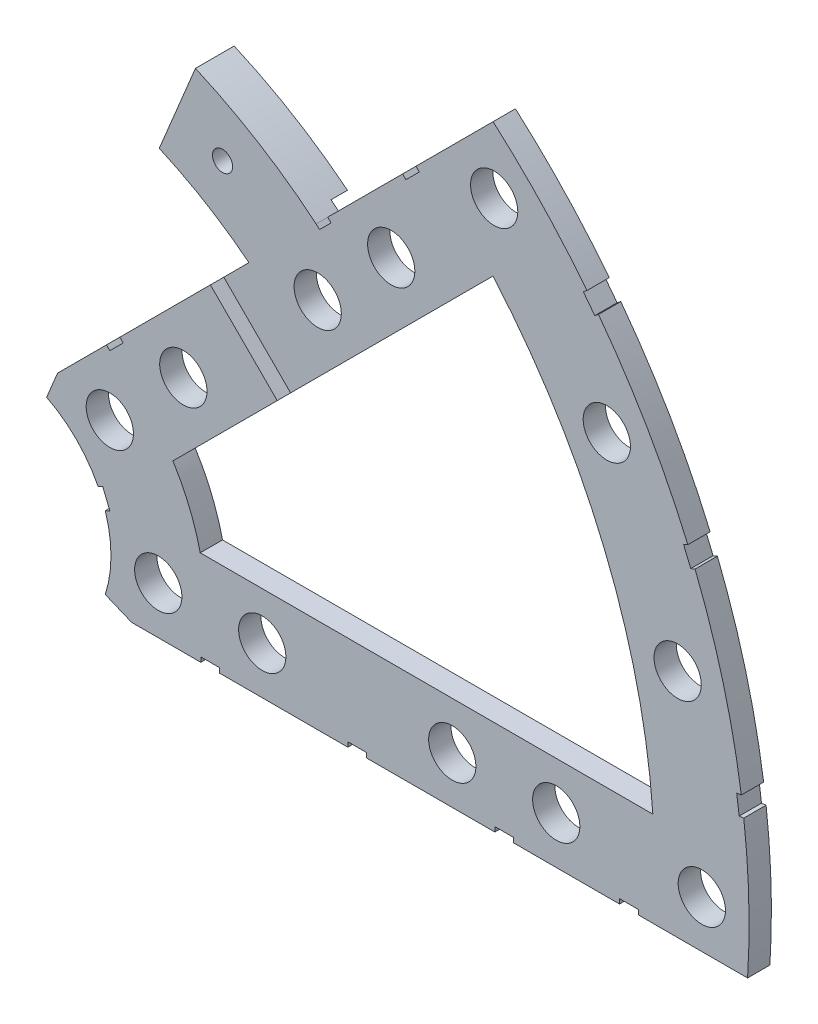
SolidWorks part; units mm, degrees
material "Brass"
ref_plane "Front Plane" through (0, 0, 0) normal (0, 0, 1) x (1, 0, 0)
ref_plane "Top Plane" through (0, 0, 0) normal (0, 1, 0) x (1, 0, 0)
ref_plane "Right Plane" through (0, 0, 0) normal (1, 0, 0) x (0, 0, -1)
sketch "Sketch1" plane through (0, 0, 0) normal (0, 0, 1) x (1, 0, 0)
  line L0 (0, 0) -> (320.3893, 0) construction
  line L1 (0, 0) -> (155.5285, 155.5285) construction
  line L2 (22.3577, 50.6576) -> (27.2188, 62.3934)
  line L3 (8.6967, 17.6769) -> (7.229, 14.1336)
  line L4 (101.4014, -6.35) -> (18.6489, -6.35)
  line L5 (15.1056, -4.8823) -> (18.6489, -6.35)
  line L6 (88.6729, 6.35) -> (27.8605, 6.35)
  line L7 (43.4342, 52.4144) -> (67.2115, 76.1917)
  line L8 (8.6967, 17.6769) -> (34.4055, 43.3857)
  line L9 (67.1914, 58.2111) -> (24.1905, 15.2102)
  line L10 (0, 0) -> (40.4486, 97.6516) construction
  line L11 (0, 0) -> (123.4567, -51.1374) construction
  line L18 (8.6967, 17.6769) -> (13.294, 8.6183) construction
  line L19 (18.6489, -6.35) -> (15.4943, 3.3063) construction
  line L20 (27.8605, 6.35) -> (27.7442, 6.7059) construction
  line L21 (24.1905, 15.2102) -> (24.3599, 14.8764) construction
  line L22 (67.2115, 76.1917) -> (8.6967, 17.6769) construction
  arc A0 (7.229, 14.1336) -> (15.1056, -4.8823) centre (0, 0) cw
  arc A1 (67.2115, 76.1917) -> (101.4014, -6.35) centre (0, 0) cw
  arc A2 (24.1905, 15.2102) -> (27.8605, 6.35) centre (0, 0) cw
  arc A3 (67.1914, 58.2111) -> (88.6729, 6.35) centre (0, 0) cw
  arc A4 (22.3577, 50.6576) -> (34.4055, 43.3857) centre (0, 0) cw
  arc A5 (27.2188, 62.3934) -> (43.4342, 52.4144) centre (0, 0) cw
  arc A8 (13.294, 8.6183) -> (15.4943, 3.3063) centre (0, 0) cw construction
  arc A9 (24.3599, 14.8764) -> (27.7442, 6.7059) centre (0, 0) cw construction
  dimension "D1" = 45
  dimension "D3" = 6.35
  dimension "D4" = 15.875
  dimension "D7" = 22.5
  dimension "D8" = 101.6
  dimension "D11" = 12.7
  dimension "D12" = 12.7
  dimension "D13" = 55.372
  dimension "D2" = 12.7
  dimension "D5" = 67.5
  dimension "D9" = 1.27
  dimension "D10" = 1.27
  dimension "D14" = 6.35
  dimension "D15" = 6.35
  dimension "D16" = 1.27
  dimension "D6" = 12.7
extrude "Boss-Extrude1" add sketch "Sketch1" along normal blind 3
sketch "Sketch2" plane through (0, 0, 3) normal (0, 0, 1) x (1, 0, 0)
  line L0 (0, 0) -> (101.6, 0) construction
  line L1 (0, 0) -> (71.842, 71.842) construction
  line L3 (0, 0) -> (22.225, 0) construction
  line L4 (0, 0) -> (15.7154, 15.7154) construction
  line L5 (0, 0) -> (95.25, 0) construction
  line L6 (0, 0) -> (92.0044, 24.6525) construction
  arc A0 (101.4014, -6.35) -> (67.2115, 76.1917) centre (0, 0) ccw construction
  circle A1 centre (22.225, 0) radius 3.175
  arc A2 (15.1056, -4.8823) -> (7.229, 14.1336) centre (0, 0) ccw construction
  circle A3 centre (36.195, 0) radius 3.175
  circle A4 centre (61.722, 0) radius 3.175
  circle A5 centre (75.692, 0) radius 3.175
  circle A6 centre (95.25, 0) radius 3.175
  circle A7 centre (15.7154, 15.7154) radius 3.175
  circle A8 centre (25.5937, 25.5937) radius 3.175
  circle A9 centre (43.644, 43.644) radius 3.175
  circle A10 centre (53.5223, 53.5223) radius 3.175
  circle A11 centre (92.0044, 24.6525) radius 3.175
  circle A12 centre (82.4889, 47.625) radius 3.175
  circle A13 centre (67.3519, 67.3519) radius 3.175
  dimension "D3" = 6.35
  dimension "D1" = 45
  dimension "D2" = 6.35
  dimension "D4" = 6.35
  dimension "D5" = 13.97
  dimension "D7" = 13.97
  dimension "D8" = 19.558
  dimension "D9" = 45
  dimension "D10" = 15
  dimension "D11" = 25.527
  dimension "D6" = 2
extrude "Cut-Extrude1" cut sketch "Sketch2" against normal through all
sketch "Sketch3" plane through (0, 0, 3) normal (0, 0, 1) x (1, 0, 0)
  line L0 (15.2664, 24.2467) -> (17.0625, 26.0427)
  line L1 (15.2664, 24.2467) -> (15.7154, 23.7977)
  line L2 (17.0625, 26.0427) -> (17.5115, 25.5937)
  line L3 (15.7154, 23.7977) -> (17.5115, 25.5937)
  line L5 (44.9911, 53.9713) -> (43.4342, 52.4144)
  line L6 (44.9911, 53.9713) -> (45.4401, 53.5223)
  line L7 (43.4342, 52.4144) -> (43.8832, 51.9654)
  line L8 (45.4401, 53.5223) -> (43.8832, 51.9654)
  line L9 (27.94, -6.35) -> (30.48, -6.35)
  line L10 (27.94, -6.35) -> (27.94, -5.715)
  line L11 (30.48, -6.35) -> (30.48, -5.715)
  line L12 (27.94, -5.715) -> (30.48, -5.715)
  line L13 (18.6489, -6.35) -> (101.4014, -6.35) construction
  line L14 (67.437, -6.35) -> (69.977, -6.35)
  line L15 (67.437, -6.35) -> (67.437, -5.715)
  line L16 (69.977, -6.35) -> (69.977, -5.715)
  line L17 (67.437, -5.715) -> (69.977, -5.715)
  line L18 (29.2307, 38.211) -> (31.0268, 40.007)
  line L19 (29.2307, 38.211) -> (38.211, 29.2307)
  line L20 (31.0268, 40.007) -> (40.007, 31.0268)
  line L21 (38.211, 29.2307) -> (40.007, 31.0268)
  line L22 (56.845, 65.8253) -> (55.049, 64.0292)
  line L23 (56.845, 65.8253) -> (57.294, 65.3763)
  line L24 (55.049, 64.0292) -> (55.498, 63.5802)
  line L25 (57.294, 65.3763) -> (55.498, 63.5802)
  line L26 (47.6885, -6.35) -> (50.2285, -6.35)
  line L27 (47.6885, -6.35) -> (47.6885, -5.715)
  line L28 (50.2285, -6.35) -> (50.2285, -5.715)
  line L29 (47.6885, -5.715) -> (50.2285, -5.715)
  line L30 (84.201, -6.35) -> (86.741, -6.35)
  line L31 (84.201, -6.35) -> (84.201, -5.715)
  line L32 (86.741, -6.35) -> (86.741, -5.715)
  line L33 (84.201, -5.715) -> (86.741, -5.715)
  line L34 (0, 0) -> (100.7308, 13.2615) construction
  line L35 (0, 0) -> (93.8662, 38.8806) construction
  line L36 (0, 0) -> (80.6047, 61.8502) construction
  line L37 (0, 0) -> (101.6, 0) construction
  line L38 (99.9355, 14.4377) -> (100.267, 11.9194)
  line L39 (99.9355, 14.4377) -> (101.1946, 14.6035)
  line L40 (100.267, 11.9194) -> (101.5261, 12.0852)
  line L41 (101.1946, 14.6035) -> (101.5261, 12.0852)
  line L42 (99.9355, 14.4377) -> (101.5261, 12.0852) construction
  line L43 (100.267, 11.9194) -> (101.1946, 14.6035) construction
  line L44 (93.7655, 37.4643) -> (94.9388, 37.9503)
  line L45 (93.7655, 37.4643) -> (92.7935, 39.811)
  line L46 (94.9388, 37.9503) -> (93.9668, 40.297)
  line L47 (92.7935, 39.811) -> (93.9668, 40.297)
  line L48 (93.7655, 37.4643) -> (93.9668, 40.297) construction
  line L49 (94.9388, 37.9503) -> (92.7935, 39.811) construction
  line L50 (79.3278, 62.4712) -> (80.874, 60.456)
  line L51 (79.3278, 62.4712) -> (80.3354, 63.2443)
  line L52 (80.874, 60.456) -> (81.8816, 61.2292)
  line L53 (80.3354, 63.2443) -> (81.8816, 61.2292)
  line L54 (79.3278, 62.4712) -> (81.8816, 61.2292) construction
  line L55 (80.874, 60.456) -> (80.3354, 63.2443) construction
  line L56 (13.5939, 7.0054) -> (14.5659, 4.6588)
  line L57 (13.5939, 7.0054) -> (14.7672, 7.4914)
  line L58 (14.5659, 4.6588) -> (15.7393, 5.1448)
  line L59 (14.7672, 7.4914) -> (15.7393, 5.1448)
  line L60 (13.5939, 7.0054) -> (15.7393, 5.1448) construction
  line L61 (14.5659, 4.6588) -> (14.7672, 7.4914) construction
  line L62 (34.4055, 43.3857) -> (8.6967, 17.6769) construction
  line L63 (67.2115, 76.1917) -> (43.4342, 52.4144) construction
  circle A0 centre (15.7154, 15.7154) radius 3.175 construction
  circle A1 centre (25.5937, 25.5937) radius 3.175 construction
  circle A2 centre (22.225, 0) radius 3.175 construction
  circle A3 centre (61.722, 0) radius 3.175 construction
  arc A4 (101.4014, -6.35) -> (67.2115, 76.1917) centre (0, 0) ccw construction
  circle A6 centre (36.195, 0) radius 3.175 construction
  circle A7 centre (53.5223, 53.5223) radius 3.175 construction
  arc A9 (15.1056, -4.8823) -> (7.229, 14.1336) centre (0, 0) ccw construction
  circle A11 centre (75.692, 0) radius 3.175 construction
  point P75 (14.6666, 6.0751)
  dimension "D2" = 5.715
  dimension "D3" = 2.54
  dimension "D8" = 0.635
  dimension "D9" = 5.715
  dimension "D12" = 5.715
  dimension "D4" = 7.5
  dimension "D5" = 22.5
  dimension "D7" = 37.5
  dimension "D10" = 90
  dimension "D11" = 1.27
  dimension "D14" = 0.635
  dimension "D15" = 90
  dimension "D18" = 0.635
  dimension "D19" = 90
  dimension "D22" = 0.635
  dimension "D20" = 1.27
  dimension "D17" = 0.635
  dimension "D21" = 12.7
  dimension "D24" = 2.54
  dimension "D6" = 5.715
  dimension "D13" = 11.4935
  dimension "D16" = 8.509
  dimension "D23" = 11.4935
  dimension "D25" = 8.509
extrude "Cut-Extrude2" cut sketch "Sketch3" against normal through all
sketch "Sketch4" plane through (0, 0, 0) normal (0, 0, -1) x (-1, 0, 0)
  line L0 (-27.2188, 62.3934) -> (-22.3577, 50.6576)
  line L1 (-42.4435, 53.2198) -> (-33.3932, 44.1696)
  line L2 (-55.049, 64.0292) -> (-44.9911, 53.9713) construction
  arc A0 (-27.2188, 62.3934) -> (-43.4342, 52.4144) centre (0, 0) ccw construction
  arc A1 (-22.3577, 50.6576) -> (-34.4055, 43.3857) centre (0, 0) ccw construction
  arc A2 (-42.4435, 53.2198) -> (-27.2188, 62.3934) centre (0, 0) cw
  arc A3 (-33.3932, 44.1696) -> (-22.3577, 50.6576) centre (0, 0) cw
  dimension "D2" = 55.372
  dimension "D3" = 68.072
  dimension "D1" = 1.27
extrude "Boss-Extrude2" add sketch "Sketch4" along normal blind 2.207
hole_wizard "#6-32 Tapped Hole1" positions "Sketch6" profile "Sketch5" tap size "#6-32" standard "ANSI Inch" end condition through all
sketch "Sketch6" plane through (0, 0, 3) normal (0, 0, 1) x (1, 0, 0)
  line L0 (0, 0) -> (67.3519, 67.3519) construction
  line L2 (0, 0) -> (30.861, 53.4528) construction
  arc A0 (43.4342, 52.4144) -> (27.2188, 62.3934) centre (0, 0) ccw construction
  point P0 (30.861, 53.4528)
  dimension "D1" = 15
  dimension "D2" = 6.35
cosmetic thread "Hole Thread1" parameters "D2"=3.5052
sketch "Sketch5" plane through (30.861, 53.4528, 3) normal (1, 0, 0) x (0, -1, 0)
  line L0 (0, 0) -> (0, 5.207)
  line L1 (0, 5.207) -> (1.3525, 5.207)
  line L2 (1.3525, 5.207) -> (1.3525, 0)
  line L5 (1.3525, 0) -> (0, 0)
  line L11 (0, -6.35) -> (0, 107.95) construction
  dimension "Thru Tap Drill Dia." = 2.7051
  dimension "Thru Tap Drill Depth" = 5.207
equation "\"LayerThick\"= 3mm"
equation "\"D1@Boss-Extrude1\"=\"LayerThick\""
equation "\"D1@Boss-Extrude2\"=.205-\"LayerThick\""
equation "\"CoilSep\"= 1.005"
equation "\"D11@Sketch2\"=\"CoilSep\""
equation "\"CoilSep2\"= \"D8@Sketch2\""
equation "\"D13@Sketch3\"=\"CoilSep\"/2-.05"
equation "\"D16@Sketch3\"=\"CoilSep2\"/2-.05"
equation "\"D23@Sketch3\"=\"CoilSep\"/2-.05"
equation "\"D25@Sketch3\"=\"CoilSep2\"/2-.05"
